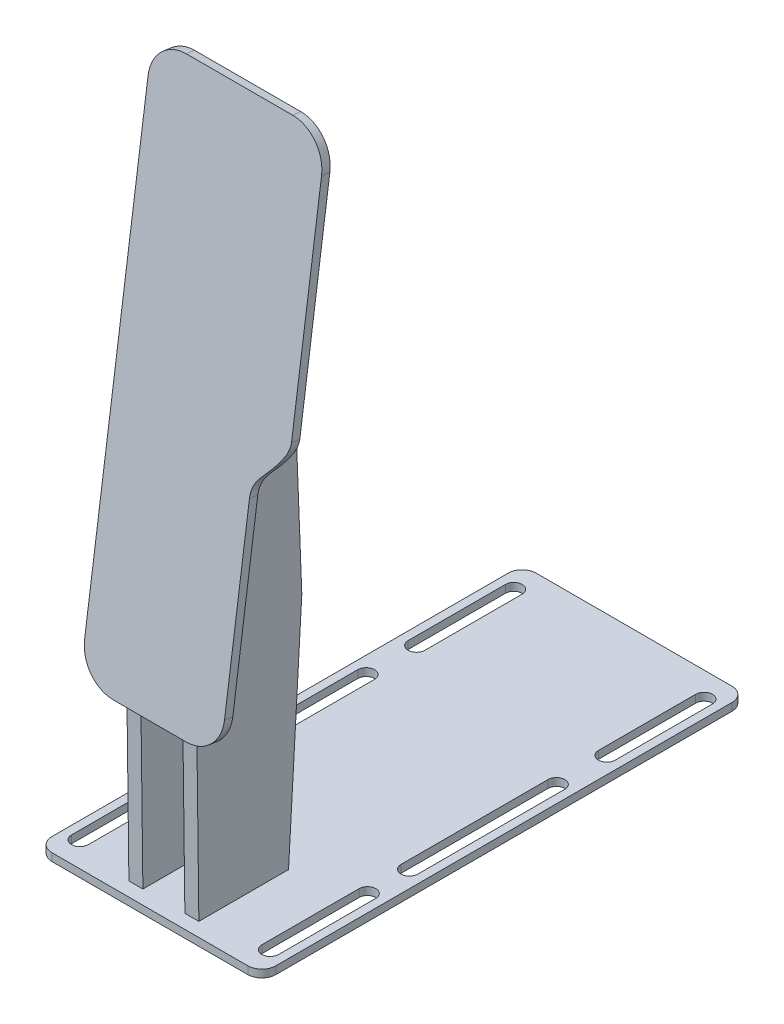
SolidWorks part; units mm, degrees
ref_plane "Front Plane" through (0, 0, 0) normal (0, 0, 1) x (1, 0, 0)
ref_plane "Top Plane" through (0, 0, 0) normal (0, 1, 0) x (1, 0, 0)
ref_plane "Right Plane" through (0, 0, 0) normal (1, 0, 0) x (0, 0, -1)
sketch "Sketch1" plane through (0, 0, 0) normal (0, 1, 0) x (1, 0, 0)
  line L0 (34, 77.5187) -> (34, 42.7687) construction
  line L1 (-35, 86.5188) -> (35, 86.5188)
  line L2 (-40, 81.5187) -> (-40, -81.5187)
  line L3 (-35, -86.5187) -> (35, -86.5187)
  line L4 (40, 81.5187) -> (40, -81.5187)
  line L5 (-40, 86.5188) -> (40, -86.5187) construction
  line L6 (-40, -86.5187) -> (40, 86.5188) construction
  line L7 (37, 77.5187) -> (37, 42.7687)
  line L8 (31, 77.5187) -> (31, 42.7687)
  line L9 (-40, 0) -> (40, 0) construction
  line L10 (0, 86.5188) -> (0, -86.5187) construction
  line L11 (-34, 77.5187) -> (-34, 42.7687) construction
  line L12 (-37, 77.5187) -> (-37, 42.7687)
  line L13 (-31, 77.5187) -> (-31, 42.7687)
  line L14 (34, -77.5187) -> (34, -42.7687) construction
  line L15 (37, -77.5187) -> (37, -42.7687)
  line L16 (31, -77.5187) -> (31, -42.7687)
  line L17 (-34, -77.5187) -> (-34, -42.7687) construction
  line L18 (-37, -77.5187) -> (-37, -42.7687)
  line L19 (-31, -77.5187) -> (-31, -42.7687)
  line L20 (34, 24.7687) -> (34, -27.7687) construction
  line L21 (37, 24.7687) -> (37, -27.7687)
  line L22 (31, 24.7687) -> (31, -27.7687)
  line L23 (-34, 24.7687) -> (-34, -27.7687) construction
  line L24 (-37, 24.7687) -> (-37, -27.7687)
  line L25 (-31, 24.7687) -> (-31, -27.7687)
  arc A0 (-40, -81.5187) -> (-35, -86.5187) centre (-35, -81.5187) ccw
  arc A1 (35, -86.5187) -> (40, -81.5187) centre (35, -81.5187) ccw
  arc A2 (35, 86.5188) -> (40, 81.5187) centre (35, 81.5187) cw
  arc A3 (-35, 86.5188) -> (-40, 81.5187) centre (-35, 81.5187) ccw
  arc A4 (37, 77.5187) -> (31, 77.5187) centre (34, 77.5187) ccw
  arc A5 (31, 42.7687) -> (37, 42.7687) centre (34, 42.7687) ccw
  arc A6 (-37, 77.5187) -> (-31, 77.5187) centre (-34, 77.5187) cw
  arc A7 (-31, 42.7687) -> (-37, 42.7687) centre (-34, 42.7687) cw
  arc A8 (37, -77.5187) -> (31, -77.5187) centre (34, -77.5187) cw
  arc A9 (31, -42.7687) -> (37, -42.7687) centre (34, -42.7687) cw
  arc A10 (-37, -77.5187) -> (-31, -77.5187) centre (-34, -77.5187) ccw
  arc A11 (-31, -42.7687) -> (-37, -42.7687) centre (-34, -42.7687) ccw
  arc A12 (37, 24.7687) -> (31, 24.7687) centre (34, 24.7687) ccw
  arc A13 (31, -27.7687) -> (37, -27.7687) centre (34, -27.7687) ccw
  arc A14 (-37, 24.7687) -> (-31, 24.7687) centre (-34, 24.7687) cw
  arc A15 (-31, -27.7687) -> (-37, -27.7687) centre (-34, -27.7687) cw
  circle A16 centre (0, -48.9201) radius 7.112
  point P0 (0, 0)
  point P20 (34, 60.1437)
  point P31 (-34, 60.1437)
  point P38 (34, -60.1437)
  point P45 (-34, -60.1437)
  point P52 (34, -1.5)
  point P59 (-34, -1.5)
  dimension "D3" = 5
  dimension "D6" = 6
  dimension "D5" = 40.75
  dimension "D9" = 12
  dimension "D10" = 9
  dimension "D1" = 80
  dimension "D2" = 173.0375
  dimension "D4" = 3
  dimension "D7" = 6
  dimension "D8" = 6
extrude "Boss-Extrude1" add sketch "Sketch1" along normal blind 2.75
sketch "Sketch2" plane through (0, 0, 0) normal (1, 0, 0) x (0, 0, -1)
  line L0 (-60.5187, 248) -> (-86.5187, 61)
  line L1 (-86.5187, 89.4829) -> (-86.5187, 186.7974) construction
  line L2 (-81.5187, 0) -> (81.5187, 0) construction
  dimension "D1" = 188.7988
  dimension "D2" = 26
  dimension "D3" = 61
  dimension "D4" = 248
  dimension "D5" = 82.084
ref_plane "Plane1" through (0, 12.9581, 93.1984) normal (0, 0.1377, 0.9905) x (0, -0.9905, 0.1377)
sketch "Sketch3" plane through (0, 12.9581, 93.1984) normal (0, 0.1377, 0.9905) x (0, -0.9905, 0.1377)
  line L0 (-237.3029, 0) -> (-48.5041, 0) construction
  line L1 (-125.3029, 25) -> (-60.5041, 25)
  line L2 (-237.3029, 25) -> (-237.3029, -13)
  line L3 (-225.3029, -25) -> (-60.5041, -25)
  line L4 (-48.5041, 13) -> (-48.5041, -13)
  line L5 (-237.3029, 0) -> (-48.5041, 0) construction
  line L6 (-225.3029, 37) -> (-147.3029, 37)
  line L7 (-147.3029, 37) -> (-125.3029, 25) construction
  arc A1 (-237.3029, -13) -> (-225.3029, -25) centre (-225.3029, -13) ccw
  arc A2 (-60.5041, -25) -> (-48.5041, -13) centre (-60.5041, -13) ccw
  arc A3 (-60.5041, 25) -> (-48.5041, 13) centre (-60.5041, 13) cw
  arc A4 (-225.3029, 37) -> (-237.3029, 25) centre (-225.3029, 25) ccw
  spline S0 degree 3 poles (-147.3029, 37) (-144.0655, 37) (-135.5828, 31) (-129.9806, 25) (-125.3029, 25) knots 0 0 0 0 0.5 1 1 1 1
  point P7 (-48.5041, 0)
  point P18 (-136.3029, 31)
  dimension "D2" = 12
  dimension "D1" = 50
  dimension "D3" = 62
  dimension "D4" = 90
  dimension "D5" = 22
extrude "Boss-Extrude2" add sketch "Sketch3" against normal blind 3 separate body
ref_plane "Plane2" through (10, 0, 0) normal (1, 0, 0) x (0, 0, -1)
sketch "Sketch4" plane through (10, 0, 0) normal (1, 0, 0) x (0, 0, -1)
  line L0 (-59.5135, 233.4453) -> (-50.5135, 232.6781)
  line L1 (-69.9415, 158.4444) -> (-59.1999, 235.7012) construction
  line L2 (-50.5135, 232.6781) -> (-44.7279, 85.6361)
  line L3 (-44.7279, 85.6361) -> (-49.4744, 2.75)
  line L4 (-81.5187, 2.75) -> (81.5187, 2.75) construction
  line L5 (-49.4744, 2.75) -> (-81.5187, 2.75)
  line L6 (-81.5187, 2.75) -> (-82.3356, 69.3021)
  line L7 (-83.5473, 60.5869) -> (-81.8948, 72.4725) construction
  line L8 (-82.3356, 69.3021) -> (-59.5135, 233.4453)
  dimension "D1" = 9
  dimension "D2" = 35
extrude "Boss-Extrude3" add sketch "Sketch4" along normal mid plane 5
mirror "Mirror1" about plane through (0, 0, 0) normal (1, 0, 0) of "Boss-Extrude3"
